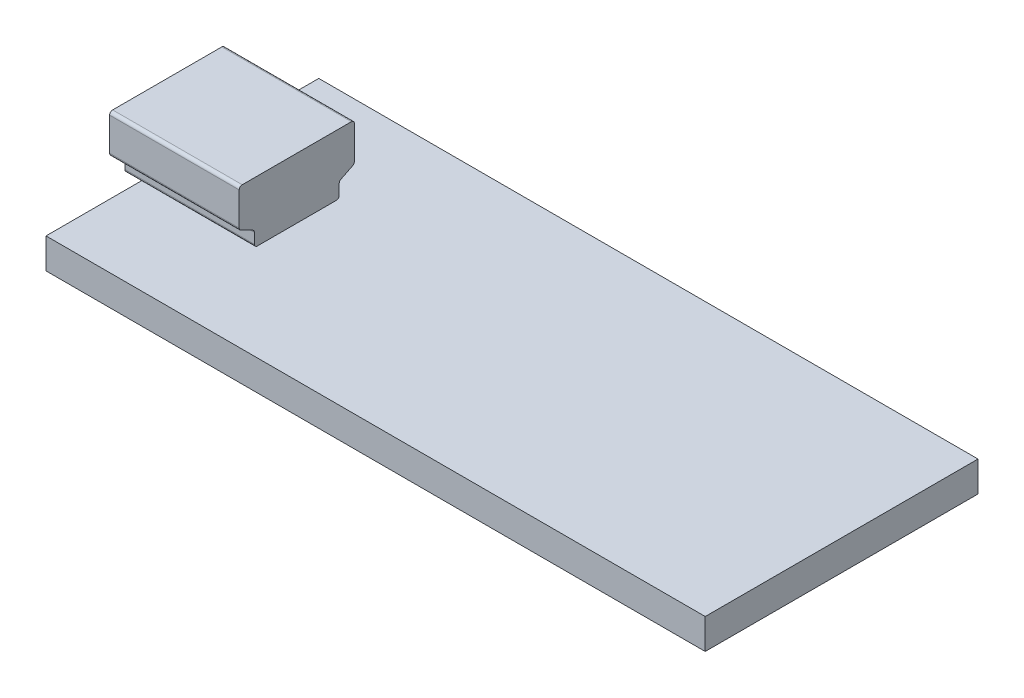
SolidWorks part; units mm, degrees
ref_plane "Front Plane" through (0, 0, 0) normal (0, 0, 1) x (1, 0, 0)
ref_plane "Top Plane" through (0, 0, 0) normal (0, 1, 0) x (1, 0, 0)
ref_plane "Right Plane" through (0, 0, 0) normal (1, 0, 0) x (0, 0, -1)
sketch "Sketch1" plane through (0, 0, 0) normal (0, 1, 0) x (1, 0, 0)
  line L1 (-21.75, 9) -> (21.75, 9)
  line L2 (-21.75, 9) -> (-21.75, -9)
  line L3 (-21.75, -9) -> (21.75, -9)
  line L4 (21.75, 9) -> (21.75, -9)
  line L5 (0, -9) -> (0, 9) construction
  line L6 (-21.75, 0) -> (21.75, 0) construction
  point P0 (0, 0)
  dimension "D1" = 43.5
  dimension "D2" = 18
extrude "Boss-Extrude1" add sketch "Sketch1" along normal blind 2
sketch "Sketch2" plane through (0, 2, 0) normal (0, 1, 0) x (1, 0, 0)
  line L0 (-21.75, 9) -> (-21.75, -9) construction
  line L1 (-14.2001, 3.8) -> (-21.75, 3.8)
  line L2 (-14.2001, 3.8) -> (-14.2001, -3.8)
  line L3 (-14.2001, -3.8) -> (-21.75, -3.8)
  line L4 (-21.75, 3.8) -> (-21.75, -3.8)
  line L5 (-17.9751, -3.8) -> (-17.9751, 3.8) construction
  line L6 (-14.2001, 0) -> (-21.75, 0) construction
  point P0 (-17.9751, 0)
  dimension "D1" = 7.6
extrude "Boss-Extrude2" add sketch "Sketch2" along normal blind 4
sketch "Sketch3" plane through (-21.75, 0, 0) normal (-1, 0, 0) x (0, 0, 1)
  line L0 (-3.6894, 3.4447) -> (-2.9106, 3.0553)
  line L1 (-2.6, 2) -> (3.8, 2)
  line L2 (-3.8, 3.6236) -> (-3.8, 5.8)
  line L3 (-3.6, 6) -> (3.6, 6)
  line L4 (3.8, 2) -> (3.8, 5.8)
  line L5 (0, 2) -> (0, 5.2629) construction
  line L6 (2.8, 2.8764) -> (2.8, 2.2)
  line L7 (-2.8, 2.8764) -> (-2.8, 2.2)
  line L8 (3.6894, 3.4447) -> (2.9106, 3.0553)
  line L25 (-19, -10) -> (19, -10)
  line L26 (19, -10) -> (19, 12)
  line L27 (19, 12) -> (13.8, 12)
  line L28 (13.8, 12) -> (13.8, 16)
  line L29 (13.8, 16) -> (-13.8, 16)
  line L30 (-13.8, 16) -> (-13.8, 12)
  line L31 (-13.8, 12) -> (-19, 12)
  line L32 (-19, 12) -> (-19, -10)
  line L33 (-19, -10) -> (19, -10)
  line L34 (19, -10) -> (19, 12)
  line L35 (19, 12) -> (13.8, 12)
  line L36 (13.8, 12) -> (13.8, 16)
  line L37 (13.8, 16) -> (-13.8, 16)
  line L38 (-13.8, 16) -> (-13.8, 12)
  line L39 (-13.8, 12) -> (-19, 12)
  line L40 (-19, 12) -> (-19, -10)
  arc A0 (-2.8, 2.2) -> (-2.6, 2) centre (-2.6, 2.2) ccw
  arc A1 (-3.8, 5.8) -> (-3.6, 6) centre (-3.6, 5.8) cw
  arc A2 (-2.9106, 3.0553) -> (-2.8, 2.8764) centre (-3, 2.8764) cw
  arc A3 (-3.6894, 3.4447) -> (-3.8, 3.6236) centre (-3.6, 3.6236) cw
  arc A4 (3.6894, 3.4447) -> (3.8, 3.6236) centre (3.6, 3.6236) ccw
  arc A5 (2.9106, 3.0553) -> (2.8, 2.8764) centre (3, 2.8764) ccw
  arc A6 (2.8, 2.2) -> (2.6, 2) centre (2.6, 2.2) cw
  arc A7 (3.6, 6) -> (3.8, 5.8) centre (3.6, 5.8) cw
  point P0 (0.5, 4)
  point P9 (-2.8, 2)
  point P12 (-3.8, 6)
  point P15 (-2.8, 3)
  point P18 (-3.8, 3.5)
  point P30 (3.8, 3.5)
  point P31 (2.8, 3)
  point P32 (2.8, 2)
  point P36 (3.8, 6)
  dimension "D1" = 0.2
  dimension "D7" = 0.2
  dimension "D2" = 7.6
  dimension "D3" = 2.5
  dimension "D4" = 1
  dimension "D5" = 1
  dimension "D6" = 10
extrude "Boss-Extrude3" add sketch "Sketch3" along normal blind 1
sketch "Sketch6" plane through (-22.75, 0, 0) normal (-1, 0, 0) x (0, 0, 1)
  line L0 (-3.6894, 3.4447) -> (-2.9106, 3.0553)
  line L1 (-3.8, 6) -> (3.8, 6)
  line L2 (-3.8, 6) -> (-3.8, 2)
  line L3 (-3.8, 2) -> (3.8, 2)
  line L4 (3.8, 6) -> (3.8, 2)
  line L5 (0, 2) -> (0, 6) construction
  line L6 (-3.8, 4) -> (3.8, 4) construction
  line L7 (-2.8, 2.8764) -> (-2.8, 2.2)
  line L8 (3.8, 6) -> (3.8, 2)
  line L9 (3.6894, 3.4447) -> (2.9106, 3.0553)
  line L10 (2.8, 2.8764) -> (2.8, 2.2)
  circle A0 centre (-3.6, 5.8) radius 0.2
  circle A1 centre (-3.6, 3.6236) radius 0.2
  circle A2 centre (-3, 2.8764) radius 0.2
  circle A3 centre (-2.6, 2.2) radius 0.2
  circle A4 centre (2.6, 2.2) radius 0.2
  circle A5 centre (3, 2.8764) radius 0.2
  circle A6 centre (3.6, 3.6236) radius 0.2
  circle A7 centre (3.6, 5.8) radius 0.2
  point P0 (0, 4)
  arc M4 (3.8, 5.8) -> (3.6, 6) centre (3.6, 5.8) ccw
  arc M6 (-3.6, 6) -> (-3.8, 5.8) centre (-3.6, 5.8) ccw
  arc M8 (-3.8, 3.6236) -> (-3.6894, 3.4447) centre (-3.6, 3.6236) ccw
  line M9 (-3.6894, 3.4447) -> (-2.9106, 3.0553)
  arc M10 (-2.9106, 3.0553) -> (-2.8, 2.8764) centre (-3, 2.8764) cw
  line M11 (-2.8, 2.8764) -> (-2.8, 2.2)
  arc M12 (-2.8, 2.2) -> (-2.6, 2) centre (-2.6, 2.2) ccw
  arc M14 (2.6, 2) -> (2.8, 2.2) centre (2.6, 2.2) ccw
  line M15 (2.8, 2.2) -> (2.8, 2.8764)
  arc M16 (2.8, 2.8764) -> (2.9106, 3.0553) centre (3, 2.8764) cw
  line M17 (2.9106, 3.0553) -> (3.6894, 3.4447)
  arc M18 (3.6894, 3.4447) -> (3.8, 3.6236) centre (3.6, 3.6236) ccw
  dimension "D1" = 4
  dimension "D2" = 7.6
extrude "Cut-Extrude1" cut sketch "Sketch6" against normal blind 15 contours A2 L2 L3 M9 M8 M12 M11 | L1 L2 M6 | A2 M10 | A5 M16 | A5 L3 L4 M17 M15 M14 M18 | L4 L1 M4
sketch "Sketch7" plane through (-22.75, 0, 0) normal (-1, 0, 0) x (0, 0, 1)
  line L16 (3.1, 5.3) -> (-3.1, 5.3)
  line L17 (-3.1, 5.3) -> (-3.1, 3.9326)
  line L18 (-3.1, 3.9326) -> (-2.5975, 3.6814)
  line L19 (-2.1, 2.8764) -> (-2.1, 2.7)
  line L20 (-2.1, 2.7) -> (2.1, 2.7)
  line L21 (2.1, 2.7) -> (2.1, 2.8764)
  line L22 (2.5975, 3.6814) -> (3.1, 3.9326)
  line L23 (3.1, 3.9326) -> (3.1, 5.3)
  line L24 (3.1, 5.3) -> (-3.1, 5.3)
  line L25 (-3.1, 5.3) -> (-3.1, 3.9326)
  line L26 (-3.1, 3.9326) -> (-2.5975, 3.6814)
  line L27 (-2.1, 2.8764) -> (-2.1, 2.7)
  line L28 (-2.1, 2.7) -> (2.1, 2.7)
  line L29 (2.1, 2.7) -> (2.1, 2.8764)
  line L30 (2.5975, 3.6814) -> (3.1, 3.9326)
  line L31 (3.1, 3.9326) -> (3.1, 5.3)
  arc A16 (-2.1, 2.8764) -> (-2.5975, 3.6814) centre (-3, 2.8764) ccw
  arc A17 (2.5975, 3.6814) -> (2.1, 2.8764) centre (3, 2.8764) ccw
  arc A18 (-2.1, 2.8764) -> (-2.5975, 3.6814) centre (-3, 2.8764) ccw
  arc A19 (2.5975, 3.6814) -> (2.1, 2.8764) centre (3, 2.8764) ccw
  dimension "D1" = 0.7
extrude "Cut-Extrude2" cut sketch "Sketch7" against normal blind 8
